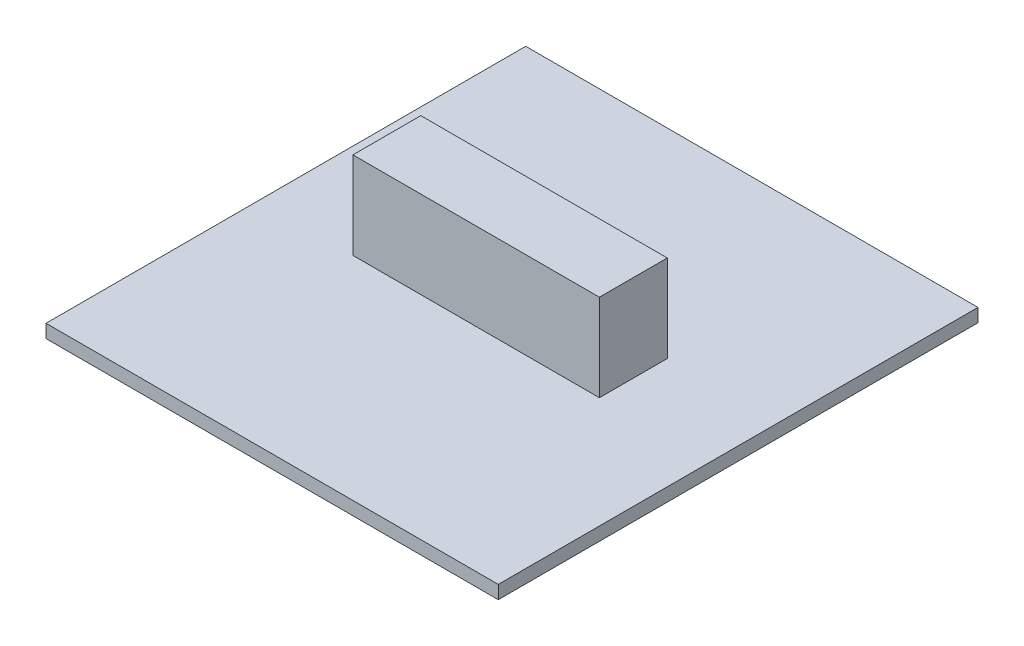
SolidWorks part; units mm, degrees
ref_plane "Front Plane" through (0, 0, 0) normal (0, 0, 1) x (1, 0, 0)
ref_plane "Top Plane" through (0, 0, 0) normal (0, 1, 0) x (1, 0, 0)
ref_plane "Right Plane" through (0, 0, 0) normal (1, 0, 0) x (0, 0, -1)
sketch "Sketch1" plane through (0, 0, 0) normal (0, 1, 0) x (1, 0, 0)
  line L1 (0, 0) -> (77.8256, 0)
  line L2 (0, 0) -> (0, -82.55)
  line L3 (0, -82.55) -> (77.8256, -82.55)
  line L4 (77.8256, 0) -> (77.8256, -82.55)
extrude "Boss-Extrude2" add sketch "Sketch1" along normal blind 2.286
sketch "Sketch2" plane through (0, 2.286, 0) normal (0, 1, 0) x (1, 0, 0)
  line L1 (16.2961, -34.3514) -> (58.7103, -34.3514)
  line L2 (16.2961, -34.3514) -> (16.2961, -46.034)
  line L3 (16.2961, -46.034) -> (58.7103, -46.034)
  line L4 (58.7103, -34.3514) -> (58.7103, -46.034)
extrude "Boss-Extrude3" add sketch "Sketch2" along normal blind 14.986
sketch "Sketch3" plane through (0, 2.286, 0) normal (0, 1, 0) x (1, 0, 0)
  text T0 "Bottom"
